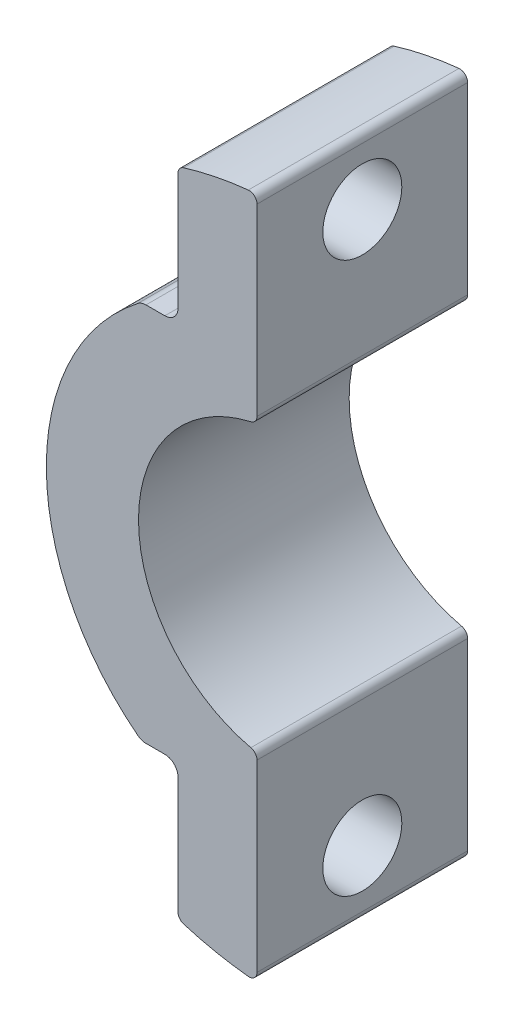
SolidWorks part; units mm, degrees
ref_plane "Plan de face" through (0, 0, 0) normal (0, 0, 1) x (1, 0, 0)
ref_plane "Plan de dessus" through (0, 0, 0) normal (0, 1, 0) x (1, 0, 0)
ref_plane "Plan de droite" through (0, 0, 0) normal (1, 0, 0) x (0, 0, -1)
sketch "Esquisse1" plane through (0, 0, 0) normal (0, 0, 1) x (1, 0, 0)
  circle A0 centre (0, 0) radius 13
  circle A1 centre (0, 0) radius 5.5
  dimension "D1" = 11
  dimension "D2" = 26
extrude "Boss.-Extru.1" add sketch "Esquisse1" along normal blind 8
sketch "Esquisse2" plane through (0, 0, 8) normal (0, 0, 1) x (1, 0, 0)
  line L1 (-1, 24.2432) -> (31.31, 24.2432)
  line L2 (-1, 24.2432) -> (-1, -25.575)
  line L3 (-1, -25.575) -> (31.31, -25.575)
  line L4 (31.31, 24.2432) -> (31.31, -25.575)
  dimension "D1" = 1
extrude "Enlèv. mat.-Extru.1" cut sketch "Esquisse2" against normal blind 8
sketch "Esquisse3" plane through (-1, 0, 0) normal (1, 0, 0) x (0, 0, -1)
  line L0 (-8, 12.9615) -> (-8, 5.4083) construction
  line L1 (-8, 12.9615) -> (0, 12.9615) construction
  line L2 (0, -12.9615) -> (-8, -12.9615) construction
  line L4 (-8, -5.4083) -> (-8, -12.9615) construction
  circle A0 centre (-4, 10.4615) radius 1.5
  circle A1 centre (-4, -10.4615) radius 1.5
  dimension "D1" = 3
  dimension "D4" = 3
  dimension "D2" = 4
  dimension "D3" = 2.5
  dimension "D5" = 2.5
  dimension "D6" = 4
extrude "Enlèv. mat.-Extru.2" cut sketch "Esquisse3" against normal blind 8
sketch "Esquisse4" plane through (0, 0, 8) normal (0, 0, 1) x (1, 0, 0)
  line L0 (-9, 8.9615) -> (-1, 8.9615) construction
  line L1 (-28.8712, 21.0445) -> (-4, 21.0445)
  line L2 (-28.8712, 21.0445) -> (-28.8712, 7.2115)
  line L3 (-28.8712, 7.2115) -> (-4, 7.2115)
  line L4 (-4, 21.0445) -> (-4, 7.2115)
  line L5 (-1, 12.9615) -> (-1, 5.4083) construction
  line L6 (-1, -5.4083) -> (-1, -12.9615) construction
  line L7 (-4, -7.2115) -> (-27.4321, -7.2115)
  line L8 (-4, -7.2115) -> (-4, -17.5209)
  line L9 (-4, -17.5209) -> (-27.4321, -17.5209)
  line L10 (-27.4321, -7.2115) -> (-27.4321, -17.5209)
  line L11 (-1, -8.9615) -> (-9, -8.9615) construction
  dimension "D1" = 1.75
  dimension "D2" = 3
  dimension "D3" = 3
  dimension "D4" = 1.75
extrude "Enlèv. mat.-Extru.3" cut sketch "Esquisse4" against normal blind 8
sketch "Esquisse6" plane through (0, 0, 8) normal (0, 0, 1) x (1, 0, 0)
  line L0 (-15.1902, -9.6723) -> (-4.6302, -7.7176)
  line L1 (-11.6345, 11.2695) -> (-4.7664, 7.6343)
  arc A0 (-4.7664, 7.6343) -> (-4.6302, -7.7176) centre (0, 0) ccw
  arc A1 (-11.6345, 11.2695) -> (-15.1902, -9.6723) centre (-4.4197, -0.7283) ccw
  point P7 (-4.6302, -7.7176)
  dimension "D1" = 9
  dimension "D2" = 14
extrude "Enlèv. mat.-Extru.4" cut sketch "Esquisse6" against normal blind 8
fillet "Congé1" radius 0.5 2 edges at (-4, -7.2115, 4) (-4, 7.2115, 4)
fillet "Congé3" radius 0.3 6 edges at (-4, -12.3693, 4) (-1, -12.9615, 4) (-1, 12.9615, 4) (-1, 5.4083, 4) (-1, -5.4083, 4) (-4, 12.3693, 4)
fillet "Congé4" radius 0.5 2 edges at (-5.3847, -7.2115, 4) (-5.3847, 7.2115, 4)
